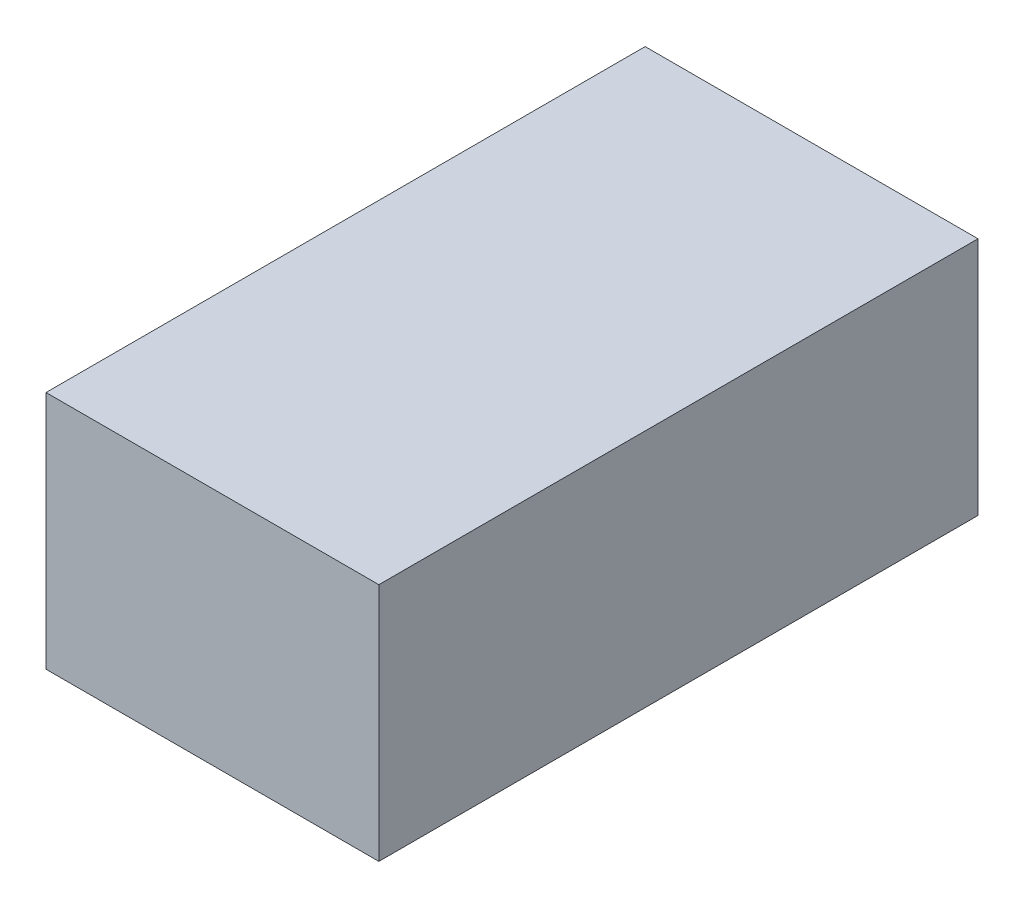
SolidWorks part; units mm, degrees
material "6061-T6 (SS)"
ref_plane "Front Plane" through (0, 0, 0) normal (0, 0, 1) x (1, 0, 0)
ref_plane "Top Plane" through (0, 0, 0) normal (0, 1, 0) x (1, 0, 0)
ref_plane "Right Plane" through (0, 0, 0) normal (1, 0, 0) x (0, 0, -1)
sketch "Sketch1" plane through (0, 0, 0) normal (0, 1, 0) x (1, 0, 0)
  line L1 (0, 0) -> (25, 0)
  line L2 (0, 0) -> (0, -45)
  line L3 (0, -45) -> (25, -45)
  line L4 (25, 0) -> (25, -45)
  dimension "D1" = 45
  dimension "D2" = 25
extrude "Boss-Extrude1" add sketch "Sketch1" along normal blind 18
